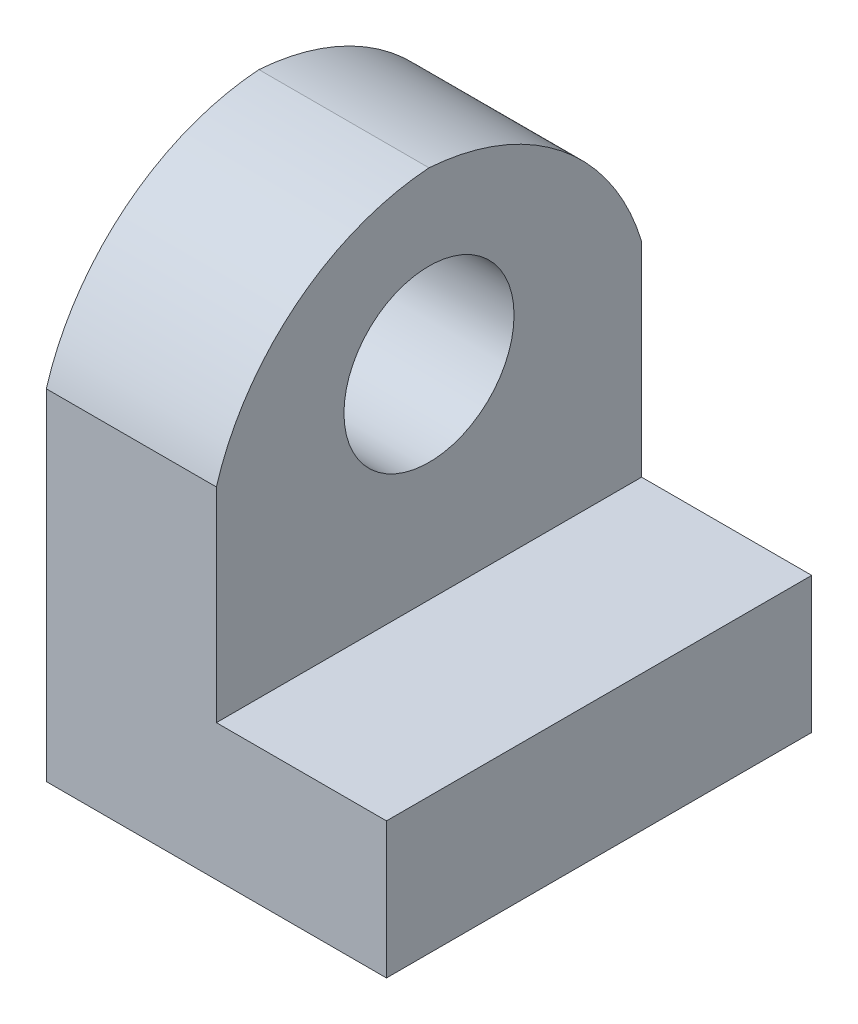
SolidWorks part; units mm, degrees
ref_plane "Alzado" through (0, 0, 0) normal (0, 0, 1) x (1, 0, 0)
ref_plane "Planta" through (0, 0, 0) normal (0, 1, 0) x (1, 0, 0)
ref_plane "Vista lateral" through (0, 0, 0) normal (1, 0, 0) x (0, 0, -1)
sketch "Croquis1" plane through (0, 0, 0) normal (0, 1, 0) x (1, 0, 0)
  line L1 (0, 0) -> (20, 0)
  line L2 (0, 0) -> (0, -25)
  line L3 (0, -25) -> (20, -25)
  line L4 (20, 0) -> (20, -25)
  dimension "D1" = 20
  dimension "D2" = 25
extrude "Saliente-Extruir1" add sketch "Croquis1" along normal blind 30
sketch "Croquis2" plane through (0, 0, 25) normal (0, 0, 1) x (1, 0, 0)
  line L0 (20, 0) -> (20, 8) construction
  line L1 (20, 30) -> (20, 0) construction
  line L2 (20, 8) -> (10, 8)
  line L3 (10, 8) -> (10, 30)
  line L6 (10, 30) -> (20, 30)
  line L7 (20, 30) -> (20, 8)
  dimension "D1" = 10
extrude "Cortar-Extruir1" cut sketch "Croquis2" against normal blind 30
sketch "Croquis6" plane through (10, 0, 0) normal (1, 0, 0) x (0, 0, -1)
  line L0 (-25, 8) -> (-25, 10) construction
  line L1 (-25, 30) -> (-25, 8) construction
  line L2 (-25, 10) -> (0, 10) construction
  line L3 (0, 30) -> (0, 8) construction
  line L4 (0, 10) -> (0, 8) construction
  line L5 (0, 8) -> (-25, 8) construction
  line L6 (-12.5, 10) -> (-12.5, 30) construction
  line L7 (-25, 10) -> (0, 10)
  line L8 (-25, 10) -> (-25, 30)
  line L9 (-25, 30) -> (0, 30)
  line L10 (0, 10) -> (0, 30)
  line L11 (-25, 20) -> (0, 20) construction
  line L12 (-25, 20) -> (-25, 30)
  line L13 (-12.5, 30) -> (0, 30)
  arc A0 (-12.5, 30) -> (0, 20) centre (-13.4892, 15.951) cw
  arc A1 (-12.5, 30) -> (-25, 20) centre (-11.5108, 15.951) ccw
  line M5 (0, 30) -> (-25, 30)
  line M6 (-25, 30) -> (-25, 8)
extrude "Cortar-Extruir3" cut sketch "Croquis6" against normal blind 30 contours A1 L9 M6 | A0 L10 M5
sketch "Croquis7" plane through (10, 0, 0) normal (1, 0, 0) x (0, 0, -1)
  line L0 (-25, 8) -> (-25, 10) construction
  line L1 (-25, 20) -> (-25, 8) construction
  line L2 (-25, 10) -> (0, 10) construction
  line L3 (0, 20) -> (0, 8) construction
  line L4 (0, 10) -> (0, 8) construction
  line L5 (0, 8) -> (-25, 8) construction
  line L6 (-12.5, 30) -> (-12.5, 10) construction
  line L7 (-25, 20) -> (0, 20) construction
  line L8 (-12.5, 30) -> (-12.5, 25) construction
  line L9 (-17.5, 25) -> (-7.5, 25) construction
  line L10 (-7.5, 25) -> (-7.5, 15) construction
  line L11 (-7.5, 15) -> (-17.5, 15) construction
  line L12 (-17.5, 15) -> (-17.5, 25) construction
  circle A0 centre (-12.5, 20) radius 5
  point P21 (-12.5, 25)
  dimension "D1" = 2
  dimension "D2" = 5
extrude "Cortar-Extruir4" cut sketch "Croquis7" against normal blind 30
